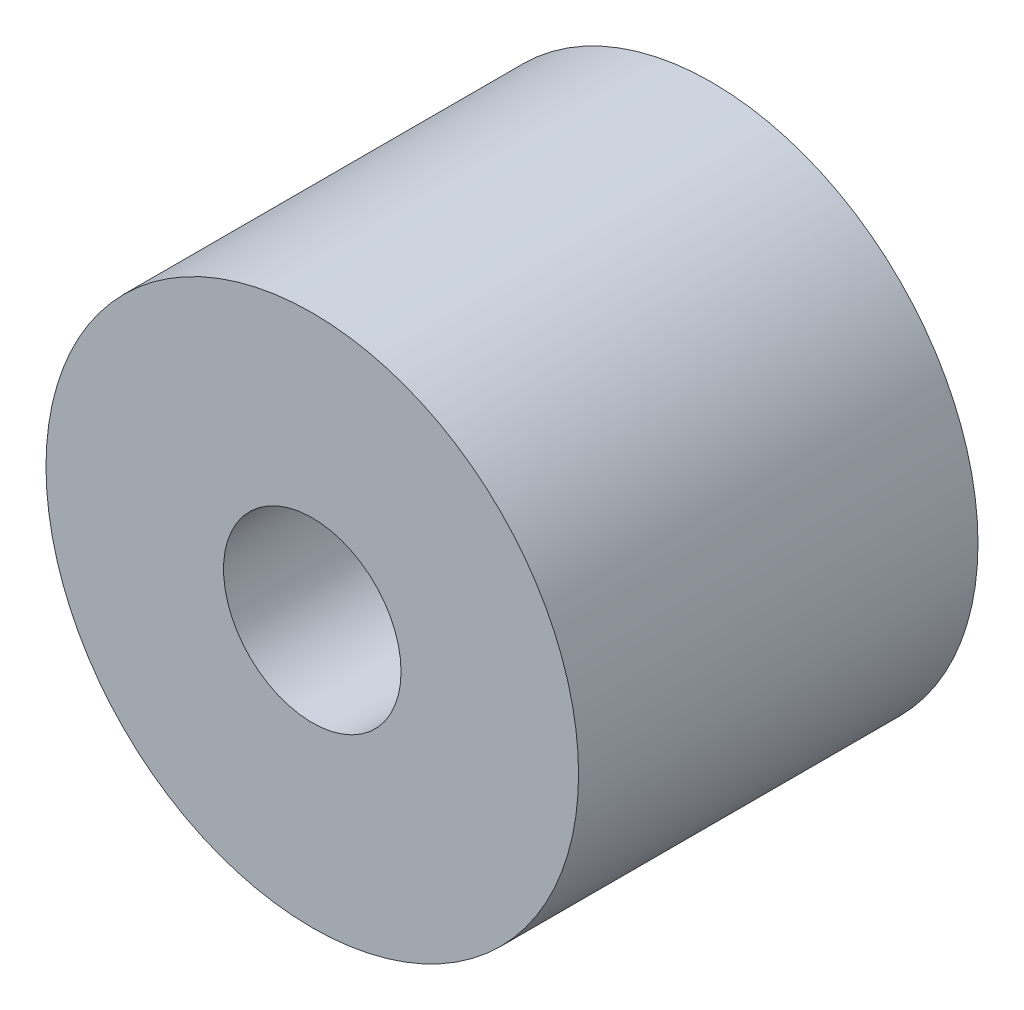
SolidWorks part; units mm, degrees
material "1060-H12"
ref_plane "Front Plane" through (0, 0, 0) normal (0, 0, 1) x (1, 0, 0)
ref_plane "Top Plane" through (0, 0, 0) normal (0, 1, 0) x (1, 0, 0)
ref_plane "Right Plane" through (0, 0, 0) normal (1, 0, 0) x (0, 0, -1)
sketch "Sketch1" plane through (0, 0, 0) normal (0, 0, 1) x (1, 0, 0)
  circle A0 centre (0, 0) radius 12
  circle A1 centre (0, 0) radius 4
extrude "Boss-Extrude1" add sketch "Sketch1" along normal blind 18
